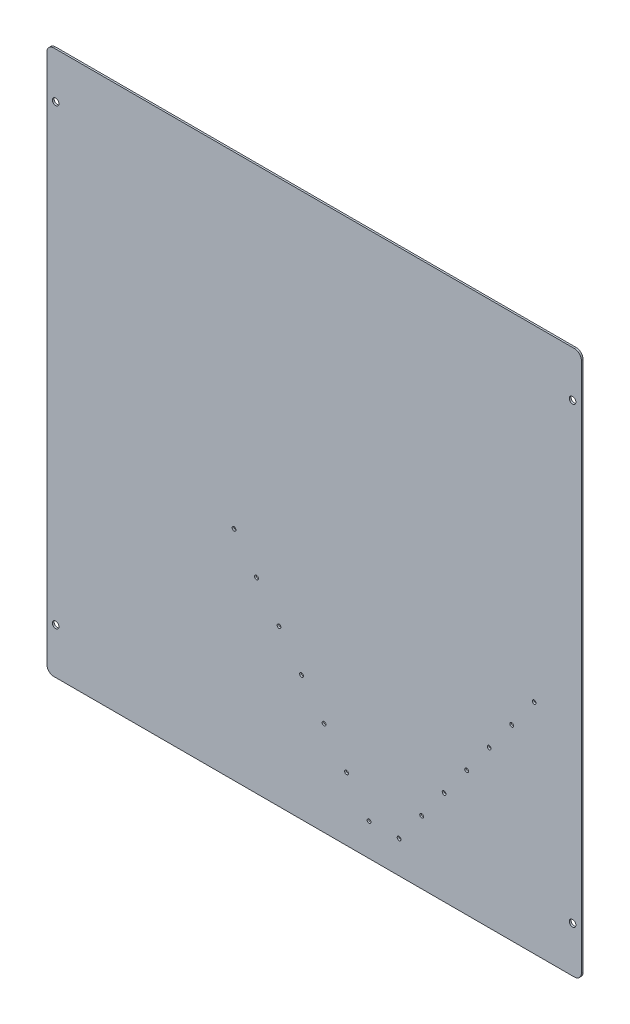
SolidWorks part; units mm, degrees
ref_plane "Front Plane" through (0, 0, 0) normal (0, 0, 1) x (1, 0, 0)
ref_plane "Top Plane" through (0, 0, 0) normal (0, 1, 0) x (1, 0, 0)
ref_plane "Right Plane" through (0, 0, 0) normal (1, 0, 0) x (0, 0, -1)
sketch "Sketch1" plane through (0, 0, 0) normal (0, 0, 1) x (1, 0, 0)
  line L1 (6.35, 0) -> (476.25, 0)
  line L2 (0, 6.35) -> (0, 485.14)
  line L3 (6.35, 491.49) -> (476.25, 491.49)
  line L4 (482.6, 6.35) -> (482.6, 485.14)
  arc A0 (0, 6.35) -> (6.35, 0) centre (6.35, 6.35) ccw
  arc A1 (476.25, 0) -> (482.6, 6.35) centre (476.25, 6.35) ccw
  arc A2 (482.6, 485.14) -> (476.25, 491.49) centre (476.25, 485.14) ccw
  arc A3 (0, 485.14) -> (6.35, 491.49) centre (6.35, 485.14) cw
  point P7 (0, 0)
  point P10 (482.6, 0)
  point P13 (482.6, 491.49)
  point P16 (0, 491.49)
  dimension "D3" = 6.35
  dimension "D1" = 482.6
  dimension "D2" = 491.49
extrude "Boss-Extrude1" add sketch "Sketch1" against normal blind 1.5875
hole_wizard "A (0.234) Diameter Hole1" positions "Sketch6" profile "Sketch7" hole size "A" standard "ANSI Inch"
sketch "Sketch6" plane through (-396.9991, -1211.1735, 0) normal (0, 0, 1) x (1, 0, 0)
  point P0 (871.6616, 1252.448)
  point P3 (871.6616, 1661.3879)
  point P5 (404.9366, 1661.3885)
  point P8 (404.9366, 1252.448)
sketch "Sketch7" plane through (474.6625, 41.2745, 0) normal (1, 0, 0) x (0, -1, 0)
  line L0 (0, 0) -> (0, 8.1356)
  line L1 (0, 8.1356) -> (2.9718, 6.35)
  line L2 (2.9718, 6.35) -> (2.9718, 0)
  line L3 (2.9718, 0) -> (0, 0)
  line L4 (0, 8.1356) -> (-2.9718, 6.35) construction
  line L5 (0, -6.35) -> (0, 107.95) construction
  dimension "Hole Dia." = 5.9436
  dimension "Hole Depth" = 6.35
  dimension "Drill Angle" = 118
hole_wizard "#29 (0.136) Diameter Hole1" positions "Sketch8" profile "Sketch9" hole size "#29" standard "ANSI Inch"
sketch "Sketch8" plane through (-437.079, -1254.719, 0) normal (0, 0, 1) x (1, 0, 0)
  point P0 (606.0677, 1451.569)
  point P3 (626.3877, 1423.629)
  point P6 (646.7077, 1395.689)
  point P9 (667.0277, 1367.749)
  point P12 (687.3477, 1339.809)
  point P15 (707.6677, 1311.869)
  point P18 (727.9877, 1283.929)
  point P21 (755.1339, 1283.929)
  point P24 (775.4539, 1311.869)
  point P27 (795.7739, 1339.809)
  point P30 (816.0939, 1367.749)
  point P33 (877.0539, 1451.569)
  point P36 (856.7339, 1423.629)
  point P39 (836.4139, 1395.689)
sketch "Sketch9" plane through (168.9887, 196.85, 0) normal (1, 0, 0) x (0, -1, 0)
  line L0 (0, 0) -> (0, 20.0878)
  line L1 (0, 20.0878) -> (1.7272, 19.05)
  line L2 (1.7272, 19.05) -> (1.7272, 0)
  line L3 (1.7272, 0) -> (0, 0)
  line L4 (0, 20.0878) -> (-1.7272, 19.05) construction
  line L5 (0, -6.35) -> (0, 107.95) construction
  dimension "Hole Dia." = 3.4544
  dimension "Hole Depth" = 19.05
  dimension "Drill Angle" = 118
